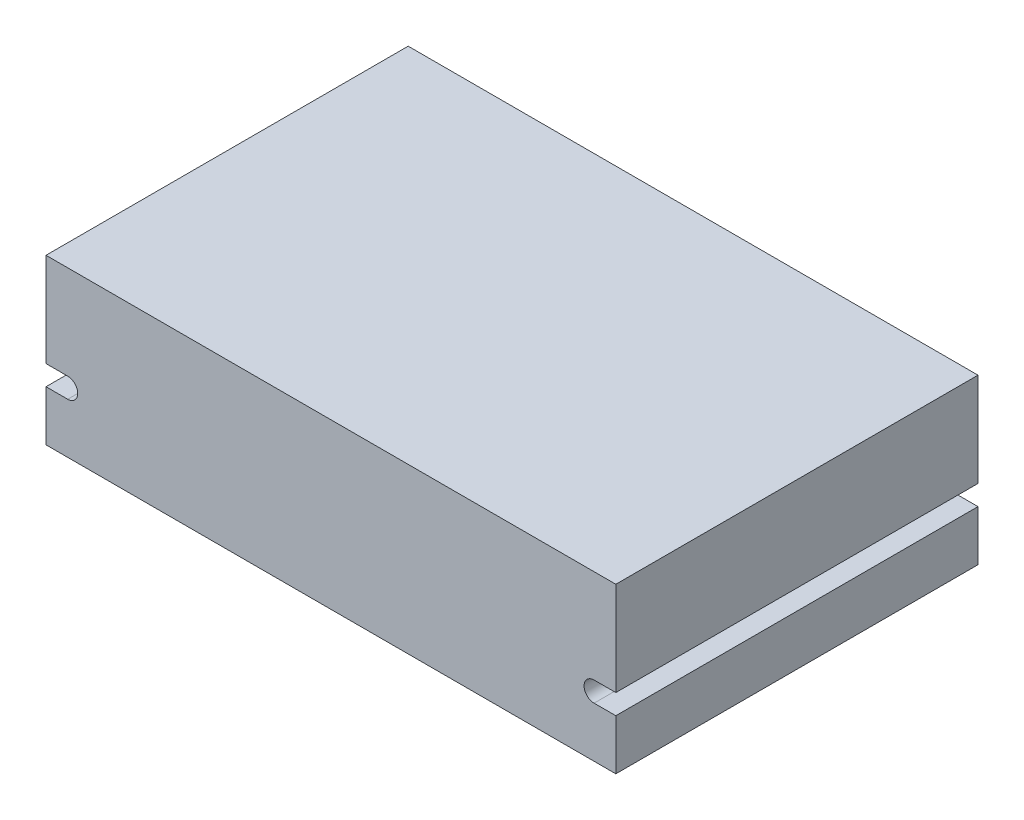
SolidWorks part; units mm, degrees
ref_plane "Piano frontale" through (0, 0, 0) normal (0, 0, 1) x (1, 0, 0)
ref_plane "Piano superiore" through (0, 0, 0) normal (0, 1, 0) x (1, 0, 0)
ref_plane "Piano destro" through (0, 0, 0) normal (1, 0, 0) x (0, 0, -1)
sketch "Schizzo1" plane through (0, 0, 0) normal (0, 0, 1) x (1, 0, 0)
  line L0 (-61.25, -4.5) -> (-52.25, -4.5) construction
  line L1 (-56.75, 17) -> (61.25, 17)
  line L2 (-56.75, 17) -> (-56.75, -2.4268)
  line L3 (-56.75, -17) -> (61.25, -17)
  line L4 (61.25, 17) -> (61.25, -2.4268)
  line L5 (-56.75, -2.4268) -> (-52.25, -2.4268)
  line L6 (-56.75, -6.5732) -> (-52.25, -6.5732)
  line L7 (-56.75, -6.5732) -> (-56.75, -17)
  line L8 (2.25, 17) -> (2.25, -17) construction
  line L9 (61.25, -6.5732) -> (56.75, -6.5732)
  line L10 (61.25, -2.4268) -> (56.75, -2.4268)
  line L11 (61.25, -6.5732) -> (61.25, -17)
  arc A0 (56.75, -6.5732) -> (56.75, -2.4268) centre (56.75, -4.5) cw
  arc A1 (-52.25, -6.5732) -> (-52.25, -2.4268) centre (-52.25, -4.5) ccw
  point P6 (-56.75, -4.5)
  dimension "D1" = 12.5
  dimension "D2" = 4.5
  dimension "D3" = 109
extrude "Estrusione-Estrusione1" add sketch "Schizzo1" along normal blind 75
